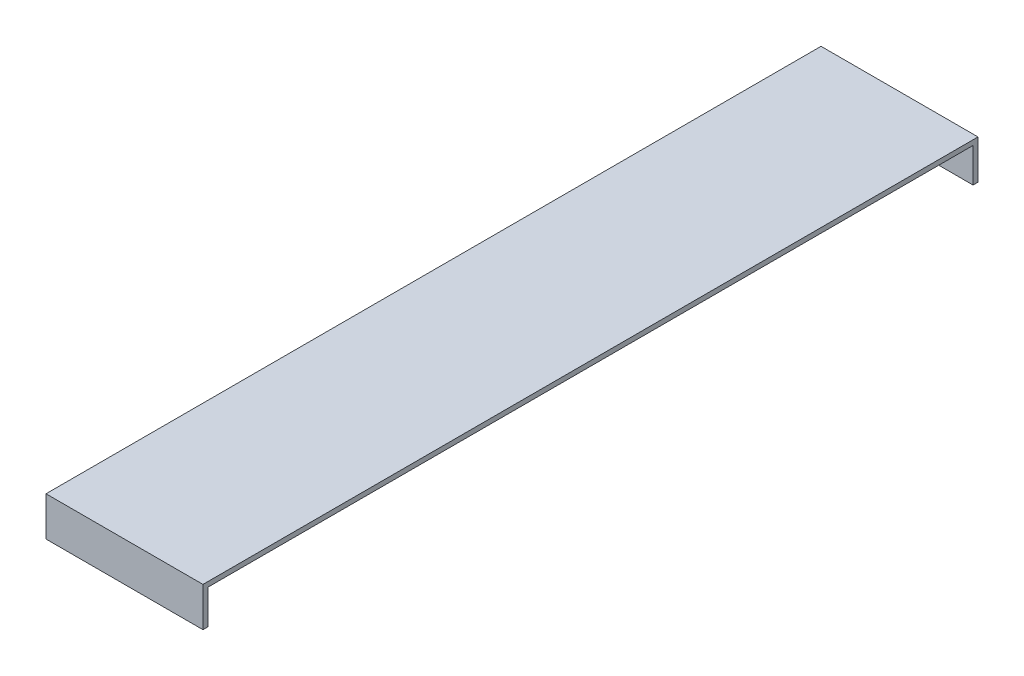
SolidWorks part; units mm, degrees
ref_plane "Front" through (0, 0, 0) normal (0, 0, 1) x (1, 0, 0)
ref_plane "Top" through (0, 0, 0) normal (0, 1, 0) x (1, 0, 0)
ref_plane "Right" through (0, 0, 0) normal (1, 0, 0) x (0, 0, -1)
sketch "Sketch1" plane through (0, 0, 0) normal (1, 0, 0) x (0, 0, -1)
  line L0 (0, 0) -> (501.65, 0)
  line L1 (0, 0) -> (0, -25.4)
  line L2 (501.65, 0) -> (501.65, -25.4)
  line L3 (3.175, -3.175) -> (3.175, -25.4)
  line L4 (3.175, -3.175) -> (498.475, -3.175)
  line L5 (498.475, -3.175) -> (498.475, -25.4)
  line L6 (0, -25.4) -> (3.175, -25.4)
  line L7 (501.65, -25.4) -> (498.475, -25.4)
  dimension "D1" = 501.65
  dimension "D2" = 25.4
  dimension "D3" = 3.175
extrude "Boss-Extrude1" add sketch "Sketch1" along normal blind 101.6
